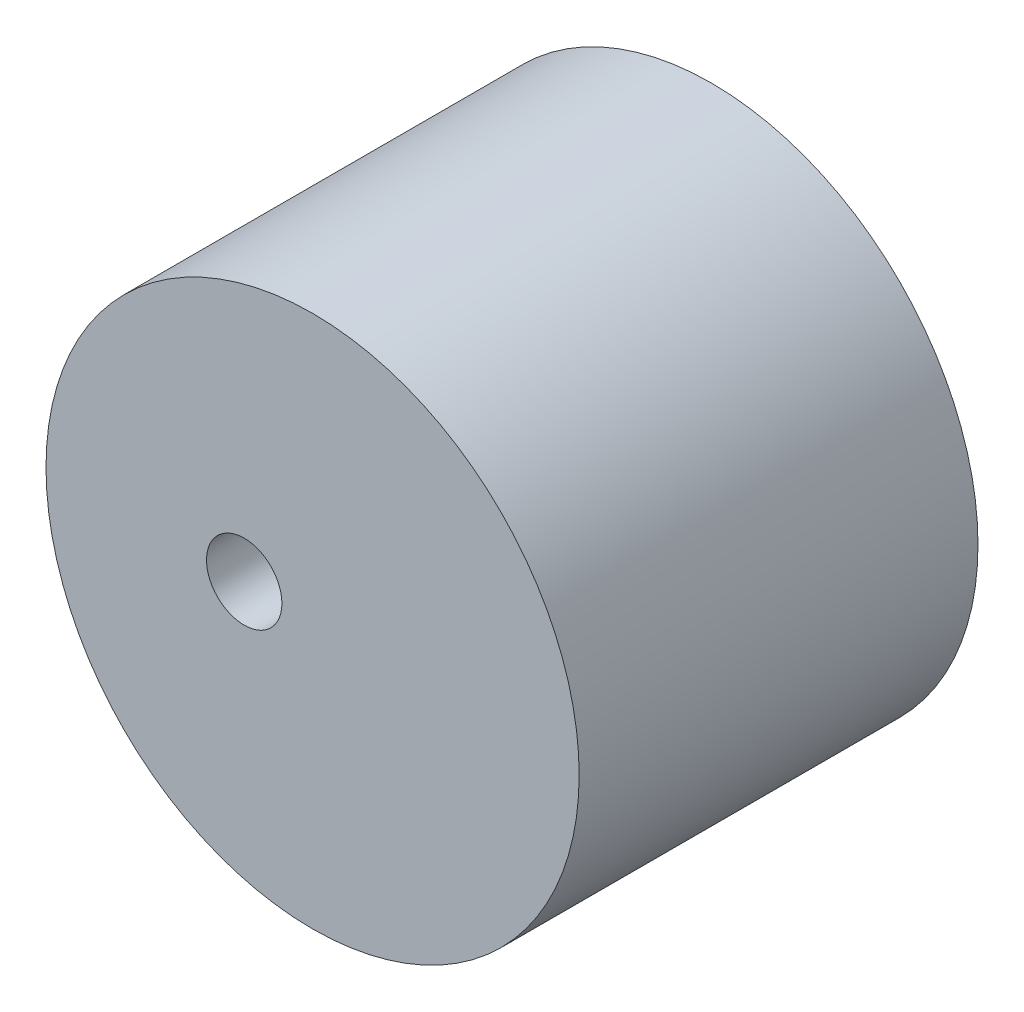
SolidWorks part; units mm, degrees
ref_plane "Front Plane" through (0, 0, 0) normal (0, 0, 1) x (1, 0, 0)
ref_plane "Top Plane" through (0, 0, 0) normal (0, 1, 0) x (1, 0, 0)
ref_plane "Right Plane" through (0, 0, 0) normal (1, 0, 0) x (0, 0, -1)
sketch "Sketch11" plane through (0, 0, 0) normal (0, 0, 1) x (1, 0, 0)
  circle A0 centre (0, 0) radius 23.3938
  circle A1 centre (-6, 0) radius 3.3085
  point P4 (0, 0)
extrude "Boss-Extrude13" add sketch "Sketch11" along normal blind 35
